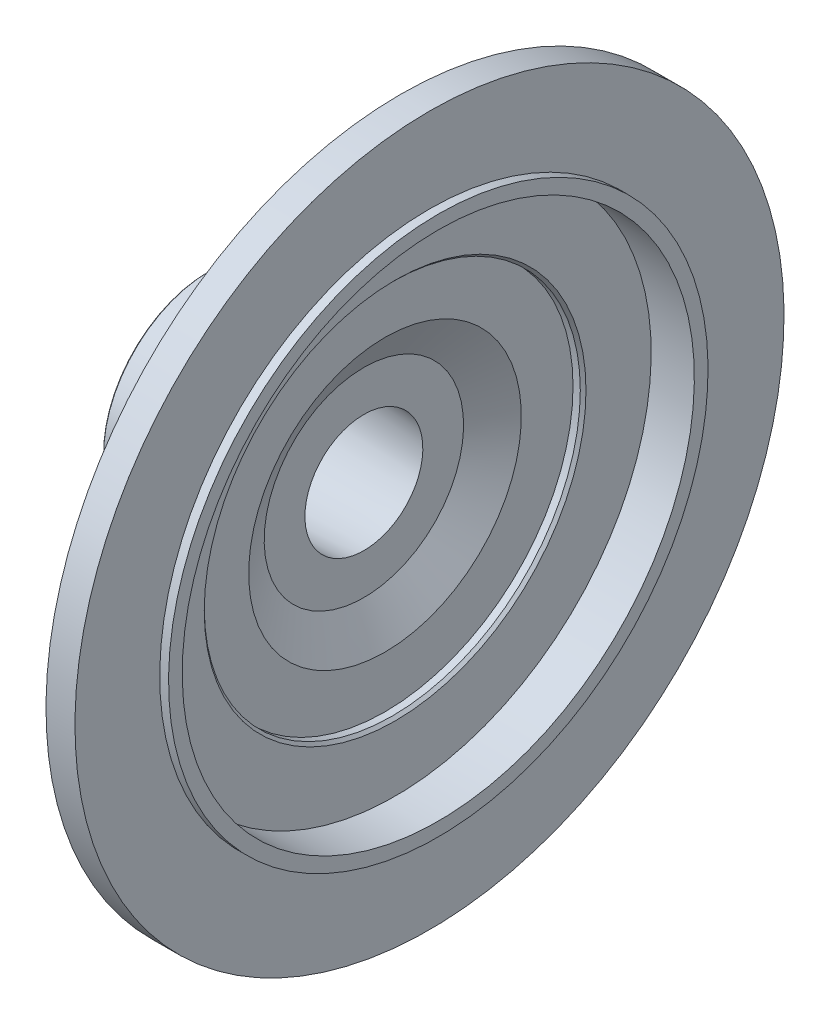
SolidWorks part; units mm, degrees
ref_plane "Front Plane" through (0, 0, 0) normal (0, 0, 1) x (1, 0, 0)
ref_plane "Top Plane" through (0, 0, 0) normal (0, 1, 0) x (1, 0, 0)
ref_plane "Right Plane" through (0, 0, 0) normal (1, 0, 0) x (0, 0, -1)
sketch "Эскиз1" plane through (0, 0, 0) normal (0, 0, 1) x (1, 0, 0)
  line L0 (0, 0) -> (-88.3676, 0) construction
  line L1 (-88.3676, 25.5972) -> (-88.3676, 36.95)
  line L2 (-87.8676, 37.45) -> (-48.0676, 37.45)
  line L3 (-86.8702, 23.9113) -> (-33.6676, 20.76)
  line L4 (-88.3676, 25.5972) -> (-86.8702, 23.9113)
  line L5 (-88.3676, 36.95) -> (-87.8676, 37.45)
  line L6 (-43.0676, 42.45) -> (-43.0676, 68.6)
  line L7 (-43.0676, 68.6) -> (-35.7676, 68.6)
  line L8 (-35.7676, 68.6) -> (-35.7676, 95.25)
  line L9 (-35.7676, 95.25) -> (-25.9176, 105.1)
  line L10 (-25.9176, 105.1) -> (-20.7676, 105.1)
  line L11 (-20.7676, 105.1) -> (-20.7676, 124.82)
  line L12 (-20.7676, 124.82) -> (-10.5676, 124.82)
  line L13 (-10.5676, 124.82) -> (-10.5676, 94.97)
  line L14 (-10.5676, 94.97) -> (-7.4676, 94.97)
  line L15 (-7.4676, 94.97) -> (-7.4676, 90.15)
  line L16 (-7.4676, 90.15) -> (-22.6676, 90.15)
  line L17 (-22.6676, 90.15) -> (-22.6676, 67.2)
  line L18 (-23.6676, 66.2) -> (-26.2276, 66.2)
  line L19 (-26.2276, 66.2) -> (-26.2276, 47.99)
  line L20 (-26.2276, 47.99) -> (-33.6676, 35.1035)
  line L21 (-33.6676, 35.1035) -> (-33.6676, 20.76)
  line L22 (-22.6676, 67.2) -> (-23.6676, 66.2)
  arc A0 (-43.0676, 42.45) -> (-48.0676, 37.45) centre (-48.0676, 42.45) cw
  point P3 (-88.3676, 24)
  point P4 (-88.3676, 37.45)
  point P7 (-33.6676, 27.9318)
  point P25 (-22.6676, 66.2)
  dimension "D8" = 5
  dimension "D1" = 24
  dimension "D2" = 1.5
  dimension "D3" = 45
  dimension "D4" = 37.45
  dimension "D5" = 0.5
  dimension "D6" = 45
  dimension "D7" = 45.3
  dimension "D9" = 68.6
  dimension "D10" = 7.3
  dimension "D11" = 95.25
  dimension "D12" = 105.1
  dimension "D13" = 45
  dimension "D14" = 124.82
  dimension "D15" = 10.2
  dimension "D16" = 5.15
  dimension "D17" = 3.1
  dimension "D18" = 94.97
  dimension "D19" = 90.15
  dimension "D20" = 66.2
  dimension "D21" = 15.2
  dimension "D22" = 3.56
  dimension "D23" = 47.99
  dimension "D24" = 35.1035
  dimension "D25" = 20.76
  dimension "D26" = 26.2
  dimension "D27" = 30
  dimension "D28" = 1
  dimension "D29" = 45
revolve "Повернуть1" add sketch "Эскиз1" angle 360 about L0
